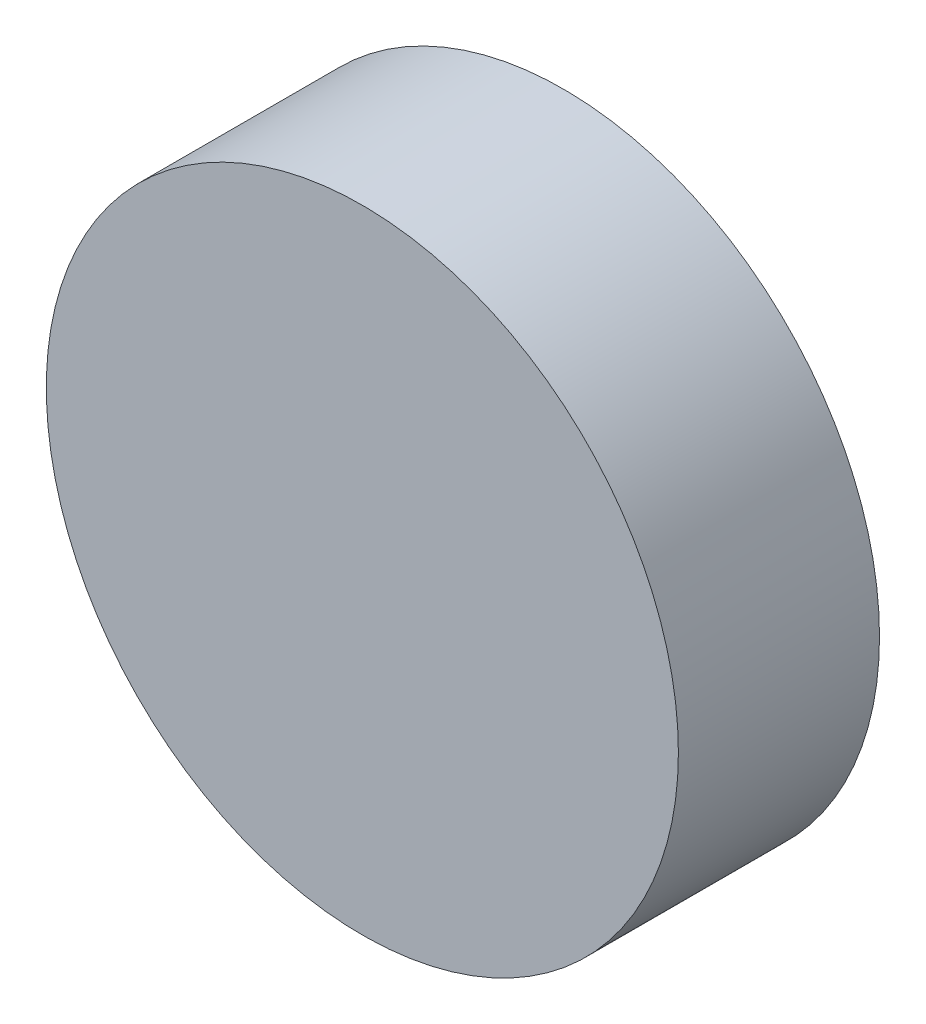
SolidWorks part; units mm, degrees
ref_plane "前视基准面" through (0, 0, 0) normal (0, 0, 1) x (1, 0, 0)
ref_plane "上视基准面" through (0, 0, 0) normal (0, 1, 0) x (1, 0, 0)
ref_plane "右视基准面" through (0, 0, 0) normal (1, 0, 0) x (0, 0, -1)
other "Configuration Table"
sketch "Sketch1" plane through (0, 0, 0) normal (0, 0, 1) x (1, 0, 0)
  circle A0 centre (0, 0) radius 11
  dimension "D1" = 22
extrude "Boss-Extrude1" add sketch "Sketch1" along normal blind 7
sketch "Sketch2" plane through (0, 0, 0) normal (0, 0, -1) x (-1, 0, 0)
  circle A0 centre (0, 0) radius 9
  dimension "D1" = 18
extrude "Cut-Extrude1" cut sketch "Sketch2" against normal blind 5
